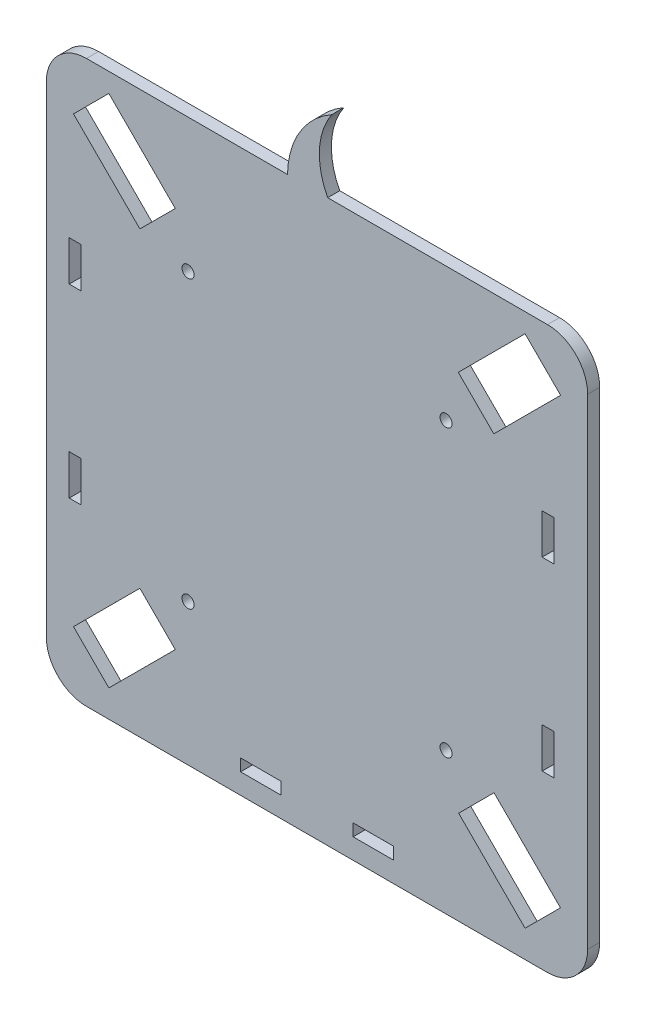
SolidWorks part; units mm, degrees
ref_plane "Alzado" through (0, 0, 0) normal (0, 0, 1) x (1, 0, 0)
ref_plane "Planta" through (0, 0, 0) normal (0, 1, 0) x (1, 0, 0)
ref_plane "Vista lateral" through (0, 0, 0) normal (1, 0, 0) x (0, 0, -1)
sketch "Model" plane through (0, 0, 0) normal (0, 0, 1) x (1, 0, 0)
  line L0 (43.9602, -45.1853) -> (43.9602, -42.1853)
  line L1 (43.9602, -42.1853) -> (53.9602, -42.1749)
  line L2 (53.9602, -42.1749) -> (53.9602, -45.1853)
  line L3 (53.9602, -45.1853) -> (43.9602, -45.1853)
  line L4 (15.9602, -45.1853) -> (15.9602, -42.1853)
  line L5 (15.9602, -42.1853) -> (25.9602, -42.1853)
  line L6 (25.9602, -42.1853) -> (25.9602, -45.1853)
  line L7 (25.9602, -45.1853) -> (15.9602, -45.1853)
  line L8 (-32.3742, -40.2583) -> (-32.3742, 79.3476)
  line L9 (-22.3742, 89.3476) -> (27.6291, 89.3476)
  line L10 (-0.287, 68.061) -> (-9.0877, 59.2604)
  line L11 (-25.6114, 75.7841) -> (-16.8107, 84.5847)
  line L12 (-9.0877, 59.2604) -> (-25.6114, 75.7841)
  line L13 (-16.8107, 84.5847) -> (-0.287, 68.061)
  line L14 (78.9595, 59.1289) -> (95.5765, 75.7459)
  line L15 (95.5765, 75.7459) -> (86.7377, 84.5847)
  line L16 (70.1207, 67.9677) -> (78.9595, 59.1289)
  line L17 (86.7377, 84.5847) -> (70.1207, 67.9677)
  line L18 (-25.6114, -34.6947) -> (-16.8107, -43.4954)
  line L19 (-9.0877, -18.171) -> (-25.6114, -34.6947)
  line L20 (-16.8107, -43.4954) -> (-0.287, -26.9717)
  line L21 (-0.287, -26.9717) -> (-9.0877, -18.171)
  line L22 (86.7377, -43.4954) -> (95.5384, -34.6948)
  line L23 (95.5384, -34.6948) -> (79.0147, -18.1711)
  line L24 (70.214, -26.9717) -> (86.7377, -43.4954)
  line L25 (79.0147, -18.1711) -> (70.214, -26.9717)
  line L26 (102.3013, 79.3476) -> (102.3013, -40.2583)
  line L27 (-22.3742, -50.2583) -> (92.3013, -50.2583)
  line L28 (37.6291, 89.3476) -> (92.3013, 89.3476)
  line L29 (90.9824, 48.5719) -> (93.9824, 48.5719)
  line L30 (90.9824, -7.5207) -> (93.9824, -7.5207)
  line L31 (-26.6809, -7.5207) -> (-23.6809, -7.5207)
  line L32 (-26.6809, 48.5719) -> (-23.6809, 48.5719)
  line L33 (93.9824, -7.5207) -> (93.9824, 2.4793)
  line L34 (93.9824, 48.5719) -> (93.9824, 38.5719)
  line L35 (-23.6809, 48.5719) -> (-23.6809, 38.5719)
  line L36 (-23.6809, -7.5207) -> (-23.6809, 2.4793)
  line L37 (93.9824, 38.5719) -> (90.9824, 38.5719)
  line L38 (93.9824, 2.4793) -> (90.9824, 2.4793)
  line L39 (-23.6809, 2.4793) -> (-26.6809, 2.4793)
  line L40 (-23.6809, 38.5719) -> (-26.6809, 38.5719)
  line L41 (90.9824, 48.5719) -> (90.9824, 38.5719)
  line L42 (-26.6809, 48.5719) -> (-26.6809, 38.5719)
  line L43 (90.9824, 2.4793) -> (90.9824, -7.5207)
  line L44 (-26.6809, 2.4793) -> (-26.6809, -7.5207)
  circle A0 centre (67.0801, -14.9991) radius 1.5
  circle A1 centre (2.885, -15.0372) radius 1.5
  circle A2 centre (2.885, 56.0883) radius 1.5
  circle A3 centre (67.0801, 56.0883) radius 1.5
  arc A4 (92.3013, -50.2583) -> (102.3013, -40.2583) centre (92.3013, -40.2583) ccw
  arc A5 (102.3013, 79.3476) -> (92.3013, 89.3476) centre (92.3013, 79.3476) ccw
  arc A6 (-22.3742, 89.3476) -> (-32.3742, 79.3476) centre (-22.3742, 79.3476) ccw
  arc A7 (-32.3742, -40.2583) -> (-22.3742, -50.2583) centre (-22.3742, -40.2583) ccw
  arc A8 (38.635, 107.7417) -> (27.6291, 89.3476) centre (49.1178, 88.9798) ccw
  arc A9 (38.635, 107.7417) -> (37.6291, 89.3476) centre (53.3935, 97.7101) ccw
extrude "Saliente-Extruir1" add sketch "Model" along normal blind 3
